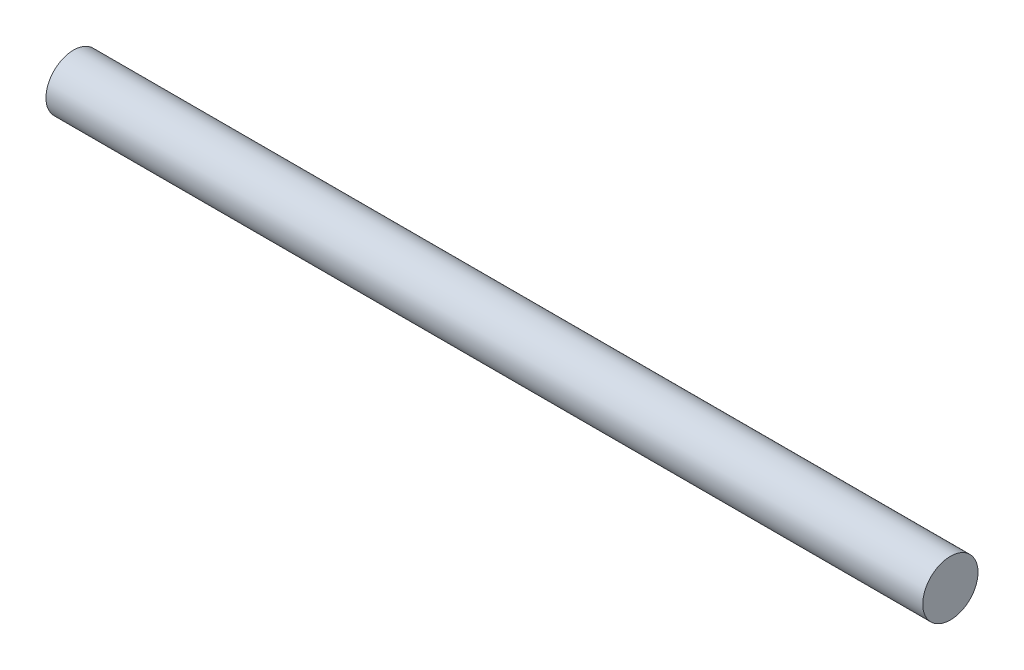
SolidWorks part; units mm, degrees
ref_plane "Front Plane" through (0, 0, 0) normal (0, 0, 1) x (1, 0, 0)
ref_plane "Top Plane" through (0, 0, 0) normal (0, 1, 0) x (1, 0, 0)
ref_plane "Right Plane" through (0, 0, 0) normal (1, 0, 0) x (0, 0, -1)
sketch "Sketch1" plane through (0, 0, 0) normal (1, 0, 0) x (0, 0, -1)
  circle A0 centre (0, 0) radius 1.575
  dimension "D1" = 3.15
extrude "Boss-Extrude1" add sketch "Sketch1" along normal blind 50
scale "Escala1" scale about origin uniform scaling yes scale factor 0.5
